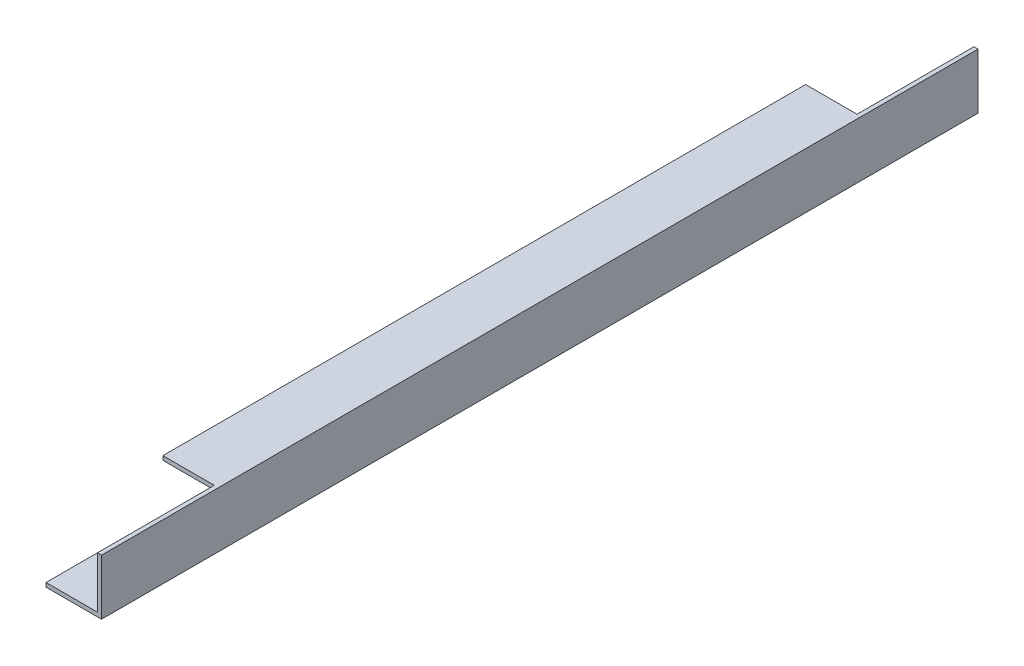
SolidWorks part; units mm, degrees
ref_plane "Front Plane" through (0, 0, 0) normal (0, 0, 1) x (1, 0, 0)
ref_plane "Top Plane" through (0, 0, 0) normal (0, 1, 0) x (1, 0, 0)
ref_plane "Right Plane" through (0, 0, 0) normal (1, 0, 0) x (0, 0, -1)
sketch "Sketch1" plane through (0, 0, 0) normal (0, 0, 1) x (1, 0, 0)
  line L0 (4.75, 4.75) -> (4.75, -4.75)
  line L1 (4.75, -4.75) -> (-4.75, -4.75)
  line L2 (4.75, 4.75) -> (-4.75, 4.75)
  line L3 (4.05, 4.05) -> (-4.75, 4.05)
  line L4 (4.05, 4.05) -> (4.05, -4.05)
  line L5 (4.05, -4.05) -> (-4.75, -4.05)
  line L6 (-4.75, 4.75) -> (-4.75, 4.05)
  line L7 (-4.75, -4.75) -> (-4.75, -4.05)
extrude "Boss-Extrude1" add sketch "Sketch1" along normal mid plane 150
sketch "Sketch2" plane through (0, 4.75, 0) normal (0, 1, 0) x (1, 0, 0)
  line L0 (4.75, -75) -> (4.75, 75) construction
  line L1 (-4.75, 75) -> (4.05, 75)
  line L2 (-4.75, 75) -> (-4.75, 55)
  line L3 (-4.75, 55) -> (4.05, 55)
  line L4 (4.05, 75) -> (4.05, 55)
  dimension "D1" = 0.7
  dimension "D2" = 20
extrude "Cut-Extrude1" cut sketch "Sketch2" against normal up to surface (0.7 mm away) up to face at (-0.35, 4.05, 0)
mirror "Mirror1" about plane through (0, 0, 0) normal (0, 0, 1) of "Cut-Extrude1"
